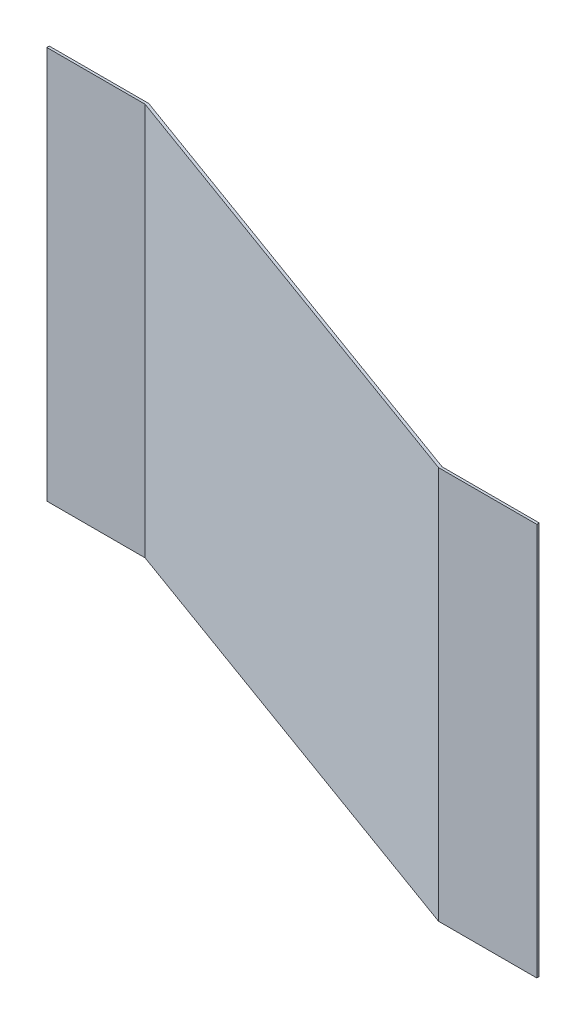
SolidWorks part; units mm, degrees
ref_plane "Front Plane" through (0, 0, 0) normal (0, 0, 1) x (1, 0, 0)
ref_plane "Top Plane" through (0, 0, 0) normal (0, 1, 0) x (1, 0, 0)
ref_plane "Right Plane" through (0, 0, 0) normal (1, 0, 0) x (0, 0, -1)
sketch "Sketch1" plane through (0, 0, 0) normal (0, 1, 0) x (1, 0, 0)
  line L0 (0, 0) -> (56.4984, 0) construction
  line L1 (56.4984, 0) -> (56.4984, -20.5637) construction
  line L2 (56.4984, -20.5637) -> (0, 0) construction
  line L4 (0, 0) -> (46983.3981, -17104.3944)
  line L5 (-120.741, -250) -> (46862.6571, -17354.3944)
  line L7 (-131.332, -250) -> (-10131.332, -250)
  line L8 (0, 0) -> (-131.332, 0)
  line L10 (-120.741, -250) -> (-131.332, -250)
  line L12 (46862.6571, -17354.3944) -> (56862.6571, -17354.3944)
  line L14 (46983.3981, -17104.3944) -> (56862.6571, -17104.3944)
  line L15 (56862.6571, -17354.3944) -> (56862.6571, -17104.3944)
  line L16 (-10131.332, -250) -> (-10131.332, 0)
  line L17 (-10131.332, 0) -> (-131.332, 0)
  dimension "D1" = 20
  dimension "D2" = 250
  dimension "D3" = 50000
  dimension "D4" = 50000
  dimension "D5" = 10000
  dimension "D6" = 10.591
  dimension "D7" = 276.221
  dimension "D8" = 131.332
  dimension "D9" = 10000
extrude "Boss-Extrude1" add sketch "Sketch1" along normal blind 40000
